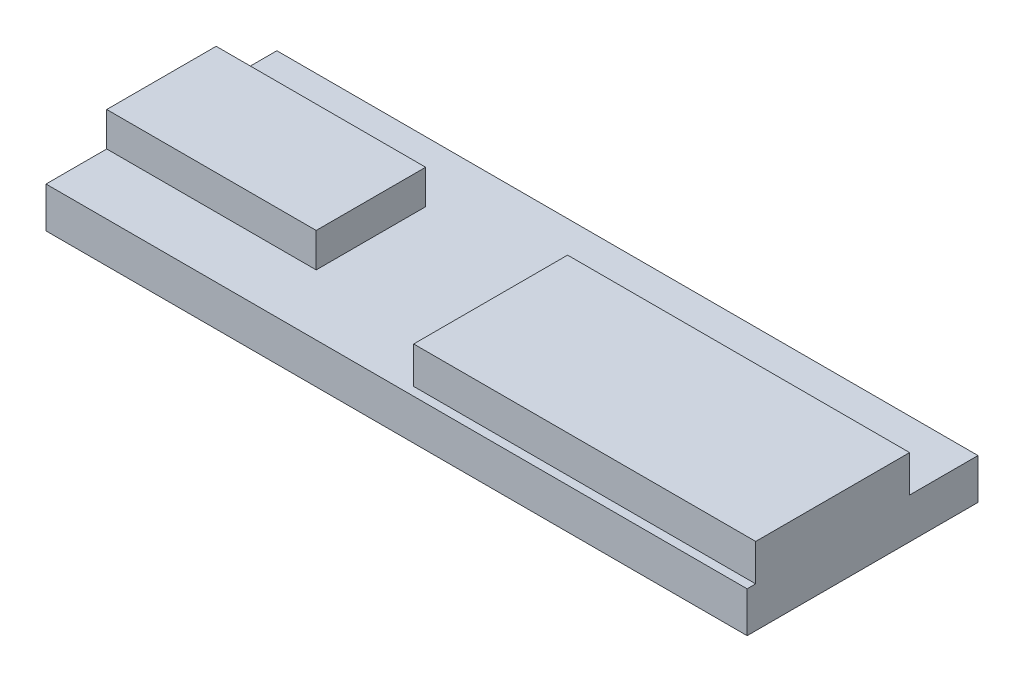
SolidWorks part; units mm, degrees
ref_plane "Front Plane" through (0, 0, 0) normal (0, 0, 1) x (1, 0, 0)
ref_plane "Top Plane" through (0, 0, 0) normal (0, 1, 0) x (1, 0, 0)
ref_plane "Right Plane" through (0, 0, 0) normal (1, 0, 0) x (0, 0, -1)
sketch "Sketch1" plane through (0, 0, 0) normal (0, 1, 0) x (1, 0, 0)
  line L1 (0, 0) -> (164, 0)
  line L2 (0, 0) -> (0, 54)
  line L3 (0, 54) -> (164, 54)
  line L4 (164, 0) -> (164, 54)
  dimension "D1" = 164
  dimension "D2" = 54
extrude "Boss-Extrude1" add sketch "Sketch1" along normal blind 9.5 contours L1 L4 L3 L2
sketch "Sketch3" plane through (0, 9.5, 0) normal (0, 1, 0) x (1, 0, 0)
  line L0 (0, 0) -> (0, 54) construction
  line L1 (0, 14.2) -> (49, 14.2)
  line L2 (0, 14.2) -> (0, 39.8)
  line L3 (0, 39.8) -> (49, 39.8)
  line L4 (49, 14.2) -> (49, 39.8)
  line L5 (0, 54) -> (164, 54) construction
  dimension "D1" = 14.2
  dimension "D2" = 25.6
  dimension "D3" = 49
extrude "Boss-Extrude2" add sketch "Sketch3" along normal blind 8
sketch "Sketch4" plane through (0, 0, 0) normal (-1, 0, 0) x (0, 0, 1)
  line L0 (-27, 0) -> (-27, 13) construction
  line L1 (0, 0) -> (-54, 0) construction
  line L3 (-30.425, 13) -> (-23.575, 13)
  line L4 (-30.425, 13) -> (-30.425, 14.8)
  line L5 (-30.425, 14.8) -> (-23.575, 14.8)
  line L6 (-23.575, 13) -> (-23.575, 14.8)
  dimension "D1" = 6.85
  dimension "D2" = 3.425
  dimension "D3" = 1.8
  dimension "D4" = 13
sketch "Sketch5" plane through (0, 9.5, 0) normal (0, 1, 0) x (1, 0, 0)
  line L0 (164, 0) -> (164, 54) construction
  line L1 (164, 2) -> (84, 2)
  line L2 (164, 2) -> (164, 38)
  line L3 (164, 38) -> (84, 38)
  line L4 (84, 2) -> (84, 38)
  dimension "D1" = 36
  dimension "D2" = 80
  dimension "D3" = 2
extrude "Boss-Extrude3" add sketch "Sketch5" along normal blind 8.6
